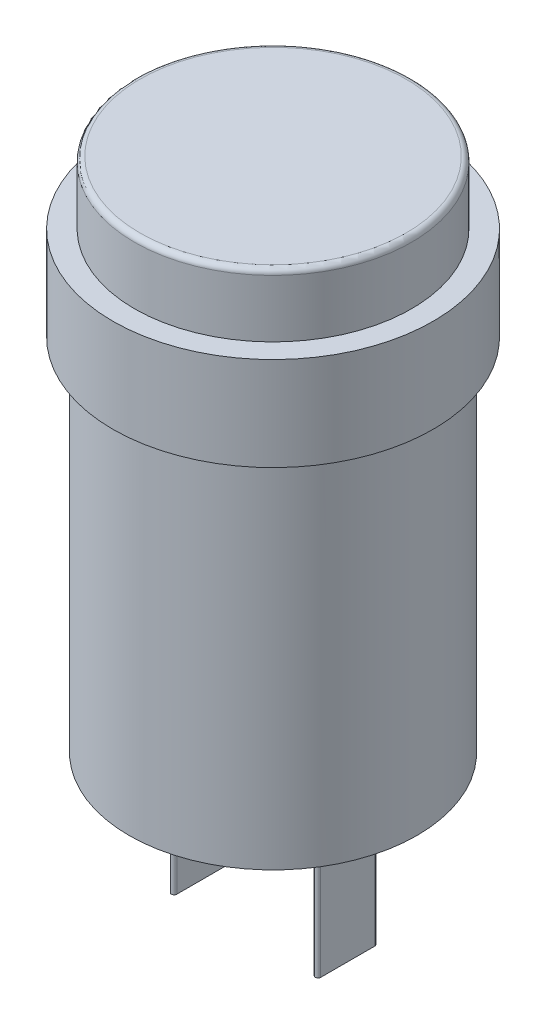
SolidWorks part; units mm, degrees
ref_plane "Front Plane" through (0, 0, 0) normal (0, 0, 1) x (1, 0, 0)
ref_plane "Top Plane" through (0, 0, 0) normal (0, 1, 0) x (1, 0, 0)
ref_plane "Right Plane" through (0, 0, 0) normal (1, 0, 0) x (0, 0, -1)
sketch "Sketch1" plane through (0, 0, 0) normal (0, 1, 0) x (1, 0, 0)
  circle A0 centre (0, 0) radius 8.9
  dimension "D1" = 17.8
extrude "Boss-Extrude1" add sketch "Sketch1" along normal blind 5.2
sketch "Sketch2" plane through (0, 0, 0) normal (0, -1, 0) x (1, 0, 0)
  circle A0 centre (0, 0) radius 8
  dimension "D1" = 16
extrude "Boss-Extrude2" add sketch "Sketch2" along normal blind 20
sketch "Sketch3" plane through (0, -20, 0) normal (0, -1, 0) x (1, 0, 0)
  line L0 (0, 0) -> (8, 0) construction
  line L1 (0, 0) -> (-8, 0) construction
  line L2 (4, 1.5) -> (4, -1.5) construction
  line L3 (4.15, 1.5) -> (4.15, -1.5)
  line L4 (3.85, 1.5) -> (3.85, -1.5)
  line L5 (-4, 1.5) -> (-4, -1.5) construction
  line L6 (-3.85, 1.5) -> (-3.85, -1.5)
  line L7 (-4.15, 1.5) -> (-4.15, -1.5)
  circle A0 centre (0, 0) radius 8 construction
  arc A1 (4.15, 1.5) -> (3.85, 1.5) centre (4, 1.5) ccw
  arc A2 (3.85, -1.5) -> (4.15, -1.5) centre (4, -1.5) ccw
  arc A3 (-3.85, 1.5) -> (-4.15, 1.5) centre (-4, 1.5) ccw
  arc A4 (-4.15, -1.5) -> (-3.85, -1.5) centre (-4, -1.5) ccw
  point P9 (4, 0)
  point P15 (-4, 0)
  dimension "D1" = 4
  dimension "D2" = 4
  dimension "D3" = 3
  dimension "D4" = 0.3
  dimension "D5" = 0.3
extrude "Boss-Extrude3" add sketch "Sketch3" along normal blind 8
sketch "Sketch4" plane through (0, 5.2, 0) normal (0, 1, 0) x (1, 0, 0)
  circle A0 centre (0, 0) radius 7.7
  dimension "D1" = 15.4
extrude "Boss-Extrude4" add sketch "Sketch4" along normal blind 3.5
sketch "Sketch6" [suppressed] plane through (-4.15, 0, 0) normal (-1, 0, 0) x (0, 0, 1)
  line L0 (0, -28) -> (0, -20) construction
  line L1 (1.5, -28) -> (-1.5, -28) construction
  line L2 (1.5, -20) -> (-1.5, -20) construction
  line L3 (1.65, -28) -> (1.65, -20) construction
  line L4 (-1.65, -26.35) -> (-1.65, -28)
  line L5 (-1.65, -28) -> (0, -28)
  line L6 (0, -28) -> (1.65, -28)
  line L7 (1.65, -28) -> (1.65, -26.35)
  arc A0 (-1.65, -26.35) -> (1.65, -26.35) centre (0, -26.35) ccw
  line M2 (-1.5, -20) -> (-1.5, -28)
  line M3 (-1.5, -28) -> (1.5, -28)
  line M4 (1.5, -28) -> (1.5, -20)
extrude "Cut-Extrude1" [suppressed] cut sketch "Sketch6" against normal through all contours A0 M3 M4 | A0 M2 M3 | A0 L6 L7 M4 | A0 L4 L5 M2
fillet "Fillet1" radius 0.3 1 edges at (0, 8.7, 7.7)
scale "Scale1" scale about centroid uniform scaling yes scale factor 1.375
